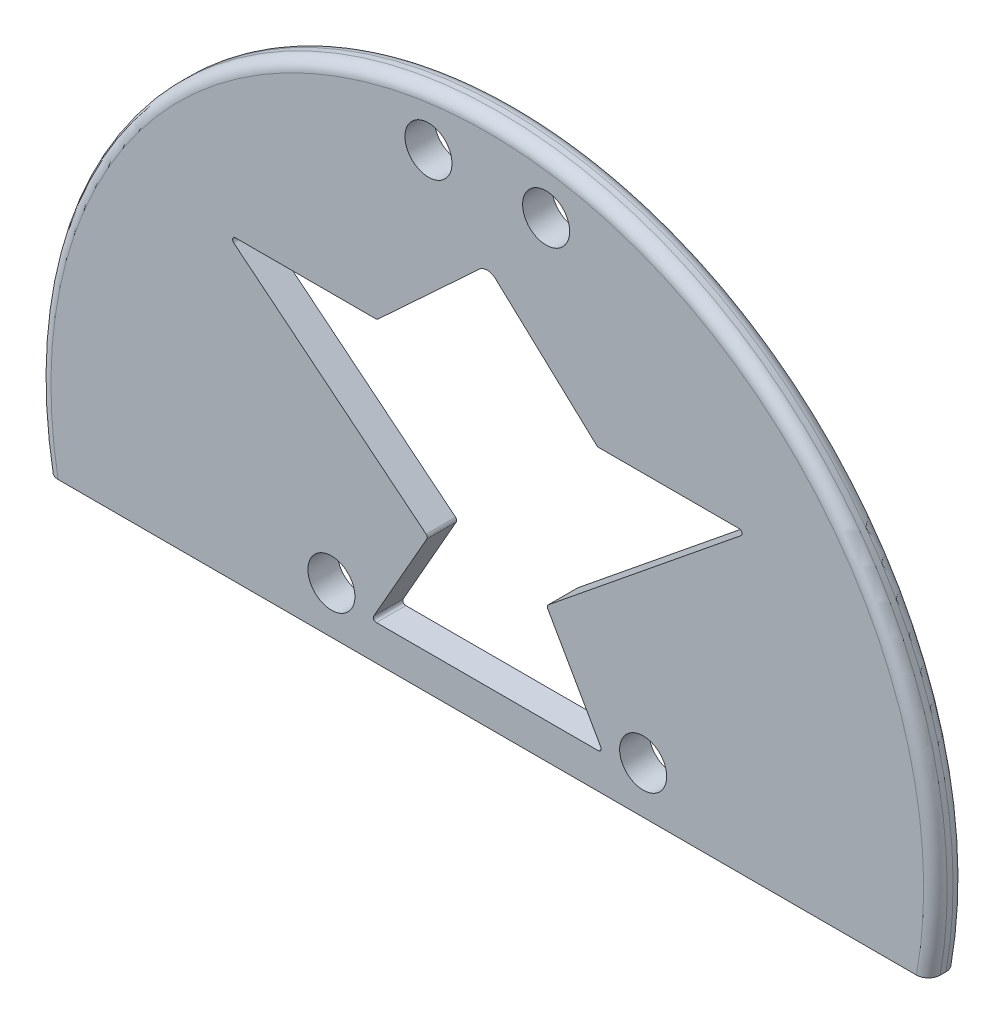
SolidWorks part; units mm, degrees
ref_plane "Front Plane" through (0, 0, 0) normal (0, 0, 1) x (1, 0, 0)
ref_plane "Top Plane" through (0, 0, 0) normal (0, 1, 0) x (1, 0, 0)
ref_plane "Right Plane" through (0, 0, 0) normal (1, 0, 0) x (0, 0, -1)
sketch "Sketch1" plane through (0, 0, 0) normal (0, 0, 1) x (1, 0, 0)
  line L0 (75, 0) -> (-75, 0) construction
  line L1 (-75, 0) -> (75, 0)
  arc A0 (-75, 0) -> (75, 0) centre (0, 13.4284) cw
  dimension "D1" = 150
extrude "Boss-Extrude1" add sketch "Sketch1" along normal blind 5
sketch "Sketch2" plane through (0, 0, 5) normal (0, 0, 1) x (1, 0, 0)
  line L0 (0, 59.8259) -> (0, -17.9819) construction
  line L1 (-75, 0) -> (75, 0) construction
  circle A0 centre (26.5, 8) radius 4
  circle A1 centre (10, 80) radius 4
  circle A2 centre (-10, 80) radius 4
  circle A3 centre (-26.5, 8) radius 4
  dimension "D3" = 8
  dimension "D4" = 8
  dimension "D1" = 53
  dimension "D2" = 8
  dimension "D5" = 10
  dimension "D6" = 80
  dimension "D7" = 72
extrude "Cut-Extrude1" cut sketch "Sketch2" against normal blind 5
sketch "Sketch3" plane through (0, 0, 5) normal (0, 0, 1) x (1, 0, 0)
  line L0 (0, 59.0103) -> (0, -14.2301) construction
  line L1 (18.8679, 5.9966) -> (-18.8679, 5.9966)
  line L2 (-19.3023, 6.7441) -> (-10.2675, 22.6044)
  line L3 (-10.3871, 23.2402) -> (-43.1183, 49.7791)
  line L4 (-42.8034, 50.6675) -> (-18.9455, 50.6675)
  line L5 (-18.6058, 50.8006) -> (-1.359, 66.7731)
  line L6 (18.6058, 50.8006) -> (1.359, 66.7731)
  line L7 (42.8034, 50.6675) -> (18.9455, 50.6675)
  line L8 (10.3871, 23.2402) -> (43.1183, 49.7791)
  line L9 (19.3023, 6.7441) -> (10.2675, 22.6044)
  arc A0 (-18.9455, 50.6675) -> (-18.6058, 50.8006) centre (-18.9455, 51.1675) ccw
  arc A1 (-10.2675, 22.6044) -> (-10.3871, 23.2402) centre (-10.702, 22.8519) ccw
  arc A2 (-18.8679, 5.9966) -> (-19.3023, 6.7441) centre (-18.8679, 6.4966) cw
  arc A3 (-43.1183, 49.7791) -> (-42.8034, 50.6675) centre (-42.8034, 50.1675) cw
  arc A4 (43.1183, 49.7791) -> (42.8034, 50.6675) centre (42.8034, 50.1675) ccw
  arc A5 (18.8679, 5.9966) -> (19.3023, 6.7441) centre (18.8679, 6.4966) ccw
  arc A6 (10.2675, 22.6044) -> (10.3871, 23.2402) centre (10.702, 22.8519) cw
  arc A7 (18.9455, 50.6675) -> (18.6058, 50.8006) centre (18.9455, 51.1675) cw
  arc A8 (-1.359, 66.7731) -> (1.359, 66.7731) centre (0, 65.3057) cw
  point P5 (-1.359, 45.711)
  point P9 (0, 0)
  point P21 (0, 5.9966)
  point P33 (0, 68.0317)
  dimension "D1" = 0.5
  dimension "D2" = 2
extrude "Cut-Extrude2" cut sketch "Sketch3" against normal blind 5
fillet "Fillet1" radius 2 2 edges at (0, 89.6211, 0) (0, 89.6211, 5)
